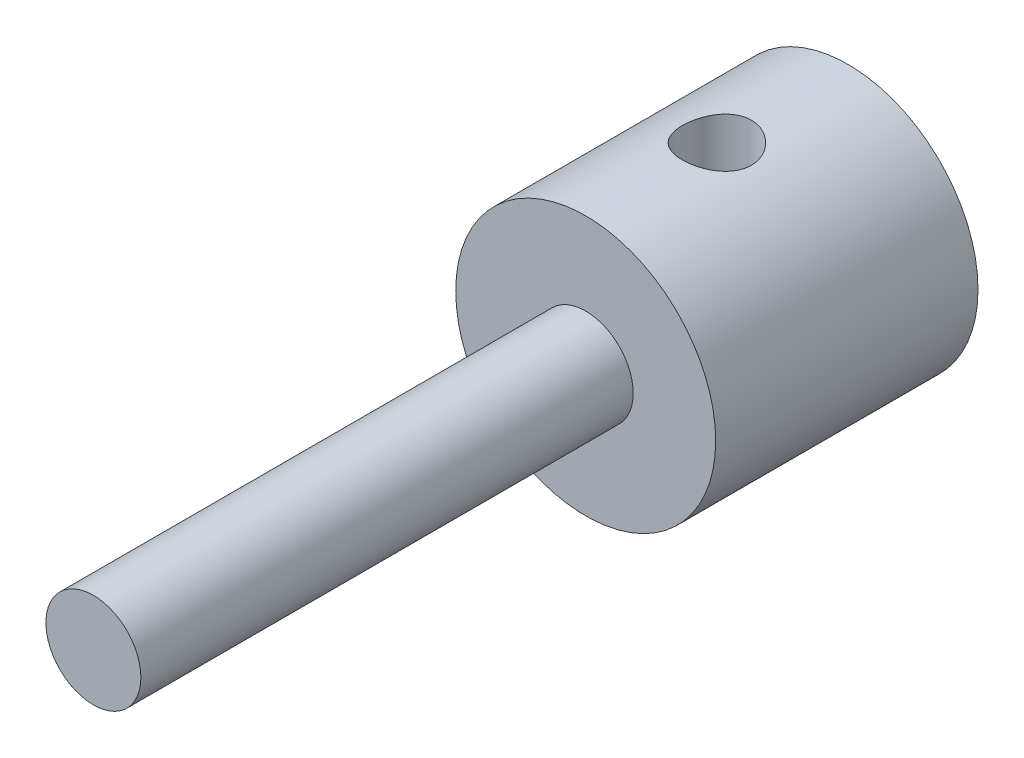
SolidWorks part; units mm, degrees
ref_plane "Front Plane" through (0, 0, 0) normal (0, 0, 1) x (1, 0, 0)
ref_plane "Top Plane" through (0, 0, 0) normal (0, 1, 0) x (1, 0, 0)
ref_plane "Right Plane" through (0, 0, 0) normal (1, 0, 0) x (0, 0, -1)
sketch "Sketch2" plane through (0, 0, 0) normal (0, 0, 1) x (1, 0, 0)
  circle A0 centre (0, 0) radius 3.062
  dimension "D1" = 6.1239
extrude "Boss-Extrude1" add sketch "Sketch2" along normal blind 31.75
sketch "Sketch3" plane through (0, 0, 0) normal (0, 0, -1) x (-1, 0, 0)
  circle A1 centre (0, 0) radius 8.382
  dimension "D1" = 16.764
extrude "Boss-Extrude2" add sketch "Sketch3" along normal blind 16.9164
sketch "Sketch4" plane through (0, 0, -16.9164) normal (0, 0, -1) x (-1, 0, 0)
  circle A0 centre (0, 0) radius 2.9972
  dimension "D1" = 5.9944
extrude "Cut-Extrude1" cut sketch "Sketch4" against normal blind 13.97
sketch "Sketch5" plane through (0, 0, 0) normal (0, 1, 0) x (1, 0, 0)
  line L0 (-8.382, 16.9164) -> (-8.382, 0) construction
  line L1 (-8.382, 16.9164) -> (-8.382, 0)
  circle A0 centre (0, 8.4582) radius 2.2225
  point P6 (-8.382, 8.4582)
  dimension "D1" = 4.445
extrude "Cut-Extrude2" cut sketch "Sketch5" along normal blind 13.97 contours A0
